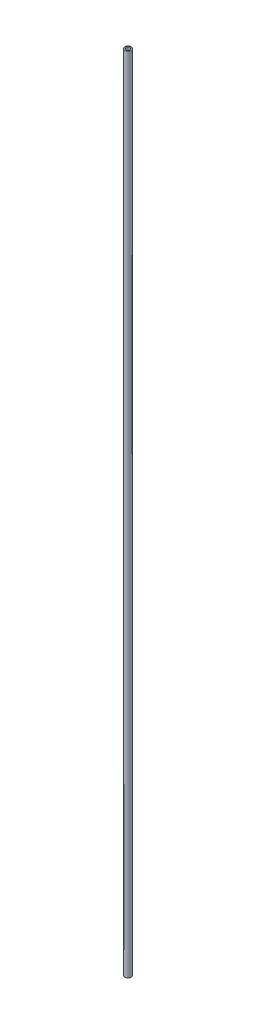
SolidWorks part; units mm, degrees
material "Commercially Pure CP-Ti UNS R50400 (SS)"
ref_plane "Front Plane" through (0, 0, 0) normal (0, 0, 1) x (1, 0, 0)
ref_plane "Top Plane" through (0, 0, 0) normal (0, 1, 0) x (1, 0, 0)
ref_plane "Right Plane" through (0, 0, 0) normal (1, 0, 0) x (0, 0, -1)
sketch "Sketch1" plane through (0, 0, 0) normal (0, 1, 0) x (1, 0, 0)
  circle A0 centre (0, 0) radius 9
  circle A1 centre (0, 0) radius 6
  dimension "D1" = 18
  dimension "D2" = 3
extrude "Boss-Extrude1" add sketch "Sketch1" along normal blind 2100 and the other way blind 200
